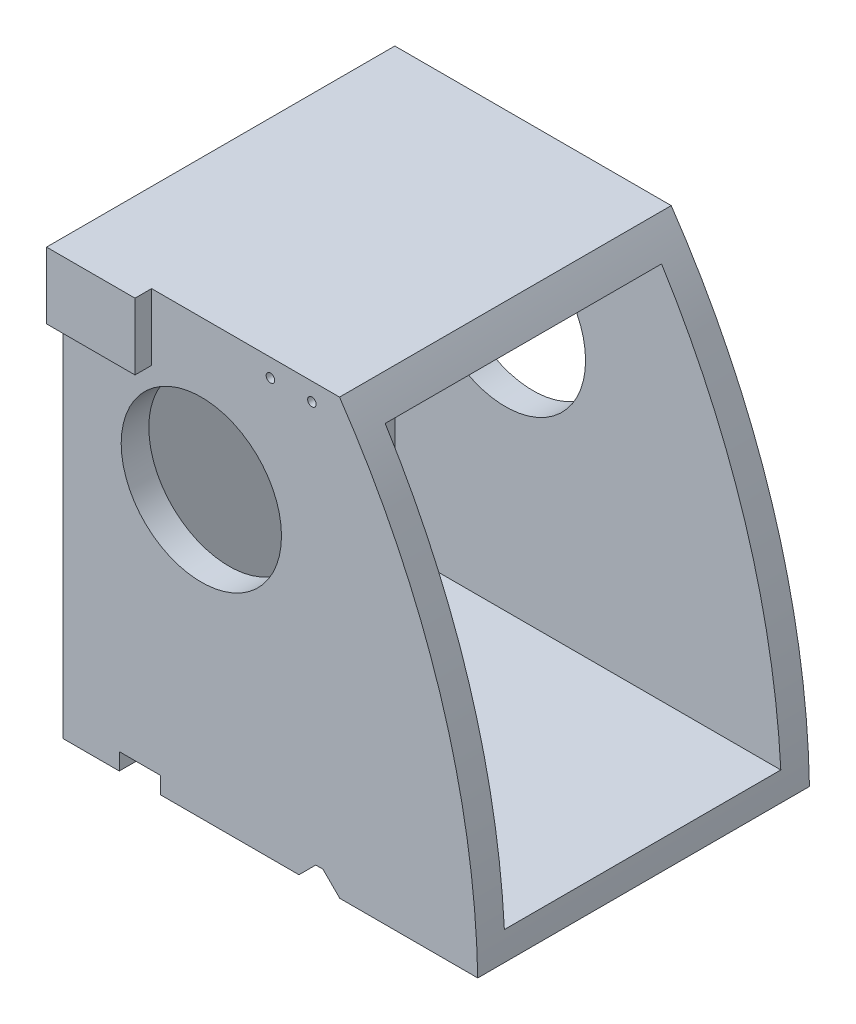
SolidWorks part; units mm, degrees
ref_plane "Front Plane" through (0, 0, 0) normal (0, 0, 1) x (1, 0, 0)
ref_plane "Top Plane" through (0, 0, 0) normal (0, 1, 0) x (1, 0, 0)
ref_plane "Right Plane" through (0, 0, 0) normal (1, 0, 0) x (0, 0, -1)
sketch "Sketch1" plane through (0, 0, 0) normal (0, 0, 1) x (1, 0, 0)
  line L1 (-10.0968, 144.4107) -> (89.9032, 144.4107)
  line L2 (-10.0968, 144.4107) -> (-10.0968, -12.5893)
  line L3 (-10.0968, -12.5893) -> (139.9032, -12.5893)
  arc A0 (89.9032, 144.4107) -> (139.9032, -12.5893) centre (-149.0036, -18.1361) cw
  dimension "D1" = 157
  dimension "D2" = 150
  dimension "D3" = 100
extrude "Boss-Extrude1" add sketch "Sketch1" along normal blind 120
shell "Shell1" thickness 10
sketch "Sketch2" plane through (0, 0, 120) normal (0, 0, 1) x (1, 0, 0)
  line L0 (89.9032, 144.4107) -> (-10.0968, 144.4107) construction
  line L1 (-10.0968, 144.4107) -> (-10.0968, -12.5893) construction
  circle A0 centre (39.9032, 90.4107) radius 29
  circle A1 centre (79.9032, 137.9107) radius 1.5432
  circle A2 centre (64.9032, 137.9107) radius 1.5432
  dimension "D1" = 54
  dimension "D2" = 50
  dimension "D3" = 6.5
  dimension "D4" = 10
  dimension "D5" = 2
extrude "Cut-Extrude1" cut sketch "Sketch2" against normal blind 200
sketch "Sketch3" plane through (0, 0, 120) normal (0, 0, 1) x (1, 0, 0)
  line L1 (-10.0968, -12.5893) -> (139.9032, -12.5893) construction
  line L5 (75.2155, -12.5893) -> (81.3007, -6.5041)
  line L6 (81.3007, -6.5041) -> (83.9032, -6.5041)
  line L7 (83.9032, -6.5041) -> (89.9884, -12.5893)
  line L8 (89.9884, -12.5893) -> (75.2155, -12.5893)
  line L10 (25.2155, -12.5893) -> (10.2155, -12.5893)
  line L11 (25.2155, -12.5893) -> (25.2155, -6.5041)
  line L12 (25.2155, -6.5041) -> (10.2155, -6.5041)
  line L13 (10.2155, -12.5893) -> (10.2155, -6.5041)
  dimension "D1" = 56
  dimension "D2" = 15
  dimension "D3" = 50
  dimension "D4" = 135
  dimension "D5" = 135
extrude "Cut-Extrude2" cut sketch "Sketch3" against normal blind 200
sketch "Sketch4" plane through (0, 0, 120) normal (0, 0, 1) x (1, 0, 0)
  line L1 (-10.0968, 144.4107) -> (21.9032, 144.4107)
  line L2 (-10.0968, 144.4107) -> (-10.0968, 120.3447)
  line L3 (-10.0968, 120.3447) -> (21.9032, 120.3447)
  line L4 (21.9032, 144.4107) -> (21.9032, 120.3447)
  dimension "D1" = 32
extrude "Boss-Extrude2" add sketch "Sketch4" along normal blind 6
